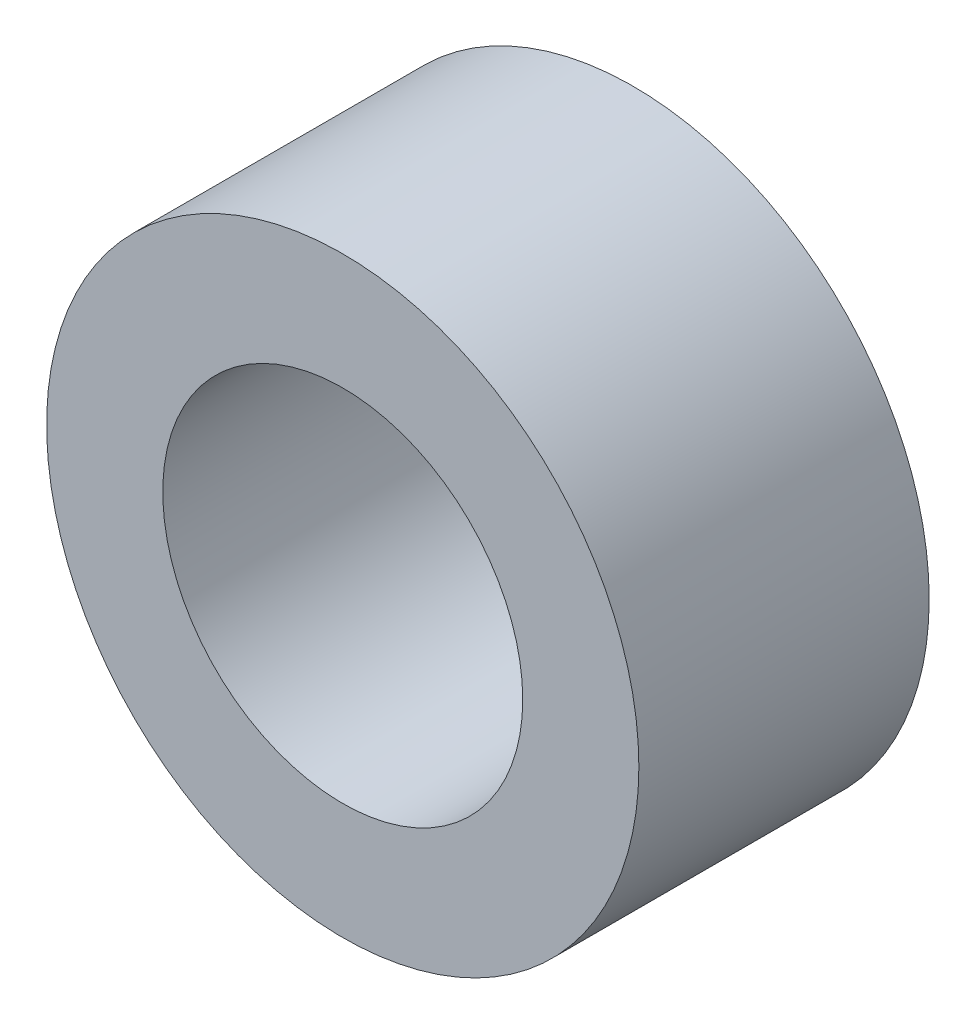
SolidWorks part; units mm, degrees
ref_plane "Front Plane" through (0, 0, 0) normal (0, 0, 1) x (1, 0, 0)
ref_plane "Top Plane" through (0, 0, 0) normal (0, 1, 0) x (1, 0, 0)
ref_plane "Right Plane" through (0, 0, 0) normal (1, 0, 0) x (0, 0, -1)
sketch "Sketch1" plane through (0, 0, 0) normal (0, 0, 1) x (1, 0, 0)
  circle A0 centre (0, 0) radius 6.2
  circle A1 centre (0, 0) radius 10.2
  dimension "D1" = 12.4
  dimension "D2" = 4
extrude "Boss-Extrude1" add sketch "Sketch1" along normal blind 10
